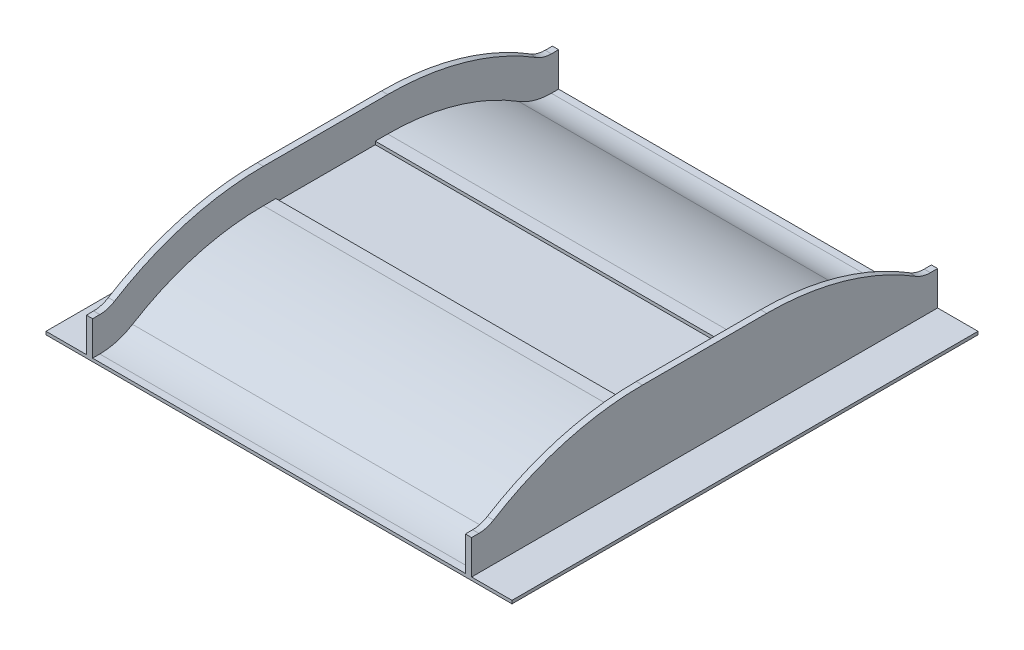
SolidWorks part; units mm, degrees
ref_plane "Front Plane" through (0, 0, 0) normal (0, 0, 1) x (1, 0, 0)
ref_plane "Top Plane" through (0, 0, 0) normal (0, 1, 0) x (1, 0, 0)
ref_plane "Right Plane" through (0, 0, 0) normal (1, 0, 0) x (0, 0, -1)
sketch "Sketch2" plane through (0, 0, 0) normal (0, 1, 0) x (1, 0, 0)
  line L1 (-750, 750) -> (750, 750)
  line L2 (-750, 750) -> (-750, -750)
  line L3 (-750, -750) -> (750, -750)
  line L4 (750, 750) -> (750, -750)
  line L5 (-750, 750) -> (750, -750) construction
  line L6 (-750, -750) -> (750, 750) construction
  point P0 (0, 0)
  dimension "D1" = 1500
  dimension "D2" = 1500
extrude "Boss-Extrude1" add sketch "Sketch2" along normal blind 10
ref_plane "Plane1" through (-620, 0, 0) normal (-1, 0, 0) x (0, 0, 1)
sketch "Sketch4" plane through (-620, 0, 0) normal (-1, 0, 0) x (0, 0, 1)
  line L0 (0, 10) -> (0, 160) construction
  line L1 (-750, 10) -> (750, 10) construction
  line L2 (-750, 160) -> (750, 160) construction
  line L3 (-726.7827, 10) -> (726.7827, 10)
  line L4 (-200, 160) -> (200, 160)
  circle A0 centre (200, -640) radius 800
  circle A1 centre (726.7827, 210) radius 200
  circle A2 centre (-726.7827, 210) radius 200
  circle A3 centre (-200, -640) radius 800
  dimension "D2" = 1600
  dimension "D3" = 400
  dimension "D1" = 150
  dimension "D4" = 400
extrude "Boss-Extrude3" add sketch "Sketch4" against normal offset from surface (1240 mm away) 130 contours L3 A3 A2 | A3 L3 A0 | A3 A0 L3 | L4 A3 A0 | A0 A3 L3 | A1 A0 L3
sketch "Sketch3" plane through (0, 10, 0) normal (0, 1, 0) x (1, 0, 0)
  line L0 (620, 750) -> (620, -750) construction
  line L1 (750, 750) -> (-750, 750) construction
  line L2 (-750, -750) -> (750, -750) construction
  line L3 (600, 750) -> (600, -750) construction
  line L4 (750, -750) -> (750, 750) construction
  line L5 (-750, -600) -> (750, -600) construction
  line L6 (-750, 750) -> (-750, -750) construction
  line L7 (-750, -620) -> (750, -620) construction
  line L8 (-750, 0) -> (750, 0) construction
  line L9 (0, 750) -> (0, -750) construction
  line L10 (-750, 620) -> (750, 620) construction
  line L11 (-750, 600) -> (750, 600) construction
  line L12 (-620, 750) -> (-620, -750) construction
  line L13 (-600, 750) -> (-600, -750) construction
  line L15 (-620, 750) -> (-600, 750)
  line L16 (-620, 750) -> (-620, -750)
  line L17 (-620, -750) -> (-600, -750)
  line L18 (-600, 750) -> (-600, -750)
  line L19 (600, 750) -> (620, 750)
  line L20 (600, 750) -> (600, -750)
  line L21 (600, -750) -> (620, -750)
  line L22 (620, 750) -> (620, -750)
  dimension "D6" = 150
  dimension "D5" = 20
  dimension "D7" = 20
  dimension "D8" = 150
sketch "Sketch5" plane through (-620, 0, 0) normal (-1, 0, 0) x (0, 0, 1)
  line L0 (-750, 10) -> (750, 10) construction
  line L1 (-750, 10) -> (750, 10)
  line L2 (-750, 120) -> (750, 120)
  line L3 (-750, 120) -> (-750, 10)
  line L4 (750, 120) -> (750, 10)
  line L7 (-200, 270) -> (200, 270)
  line L8 (-200, 270) -> (200, 270)
  arc A11 (679.3722, 133.5) -> (726.7827, 120) centre (726.7827, 210) ccw
  arc A12 (679.3722, 133.5) -> (200, 270) centre (200, -640) ccw
  arc A13 (-200, 270) -> (-679.3722, 133.5) centre (-200, -640) ccw
  arc A14 (-726.7827, 120) -> (-679.3722, 133.5) centre (-726.7827, 210) ccw
  arc A15 (679.3722, 133.5) -> (726.7827, 120) centre (726.7827, 210) ccw
  arc A16 (679.3722, 133.5) -> (200, 270) centre (200, -640) ccw
  arc A17 (-200, 270) -> (-679.3722, 133.5) centre (-200, -640) ccw
  arc A18 (-726.7827, 120) -> (-679.3722, 133.5) centre (-726.7827, 210) ccw
  dimension "D1" = 110
  dimension "D2" = 110
extrude "Boss-Extrude4" add sketch "Sketch5" against normal blind 20
mirror "Mirror1" about plane through (0, 0, 0) normal (1, 0, 0) of "Boss-Extrude4"
sketch "Sketch6" plane through (0, 160, 0) normal (0, 1, 0) x (1, 0, 0)
  line L0 (600, 200) -> (600, -200) construction
  line L1 (-600, 160) -> (600, 160)
  line L2 (-600, 160) -> (-600, -160)
  line L3 (-600, -160) -> (600, -160)
  line L4 (600, 160) -> (600, -160)
  line L5 (-600, 160) -> (600, -160) construction
  line L6 (-600, -160) -> (600, 160) construction
  line L7 (600, 200) -> (-600, 200) construction
  point P0 (0, 0)
  dimension "D1" = 40
extrude "Cut-Extrude1" cut sketch "Sketch6" against normal blind 10
equation "\"CellSize\"=1500"
equation "\"D1@Sketch2\"=\"CellSize\""
equation "\"D2@Sketch2\"=\"CellSize\""
equation "\"TrackWidth\"= 1200"
equation "\"C\"=342.079"
equation "\"WallWidth\"=20"
equation "\"D6@Sketch3\"=\"EdgeWidth\""
equation "\"D5@Sketch3\"=\"WallWidth\""
equation "\"D7@Sketch3\"=\"WallWidth\""
equation "\"EdgeWidth\"= ( \"CellSize\" - \"TrackWidth\" ) / 2"
equation "\"D8@Sketch3\"=\"EdgeWidth\""
